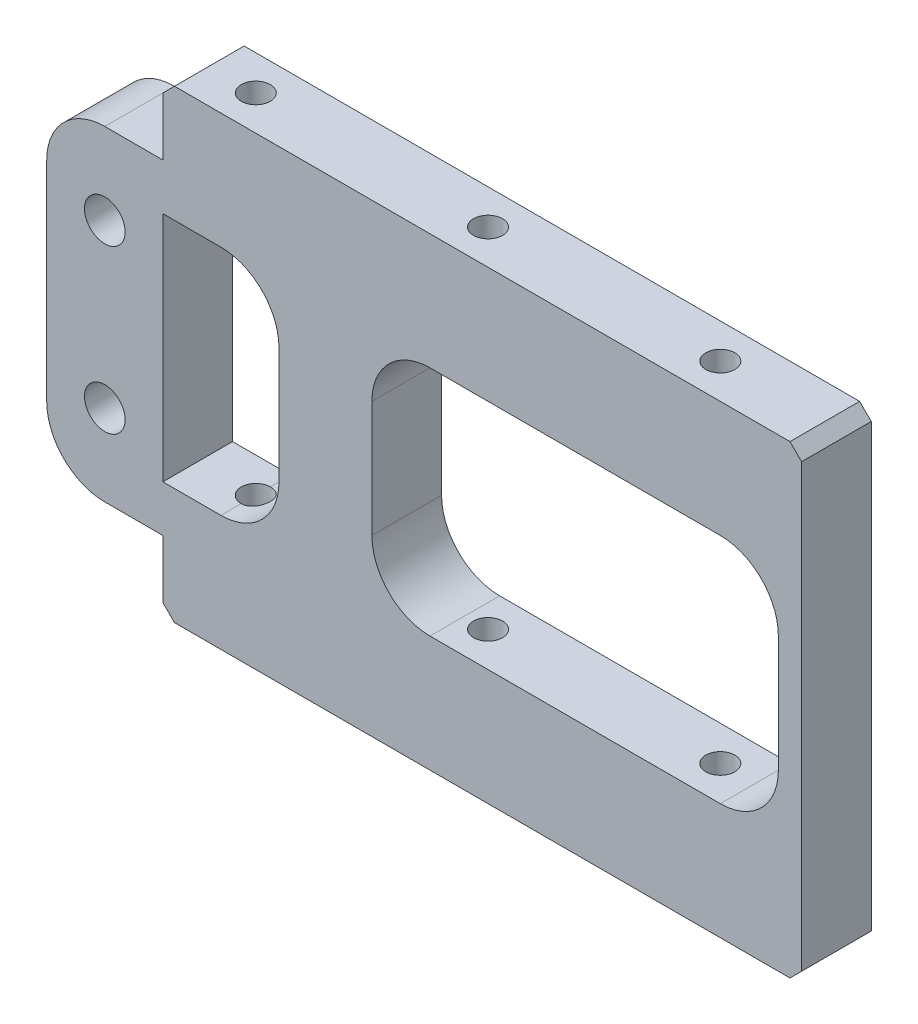
SolidWorks part; units mm, degrees
ref_plane "Front Plane" through (0, 0, 0) normal (0, 0, 1) x (1, 0, 0)
ref_plane "Top Plane" through (0, 0, 0) normal (0, 1, 0) x (1, 0, 0)
ref_plane "Right Plane" through (0, 0, 0) normal (1, 0, 0) x (0, 0, -1)
sketch "Sketch1" plane through (0, 0, 0) normal (0, 1, 0) x (1, 0, 0)
  line L1 (-27.5, 3) -> (27.5, 3)
  line L2 (-27.5, 3) -> (-27.5, -3)
  line L3 (-27.5, -3) -> (27.5, -3)
  line L4 (27.5, 3) -> (27.5, -3)
  line L5 (-27.5, 3) -> (27.5, -3) construction
  line L6 (-27.5, -3) -> (27.5, 3) construction
  point P0 (0, 0)
  dimension "D1" = 6
  dimension "D2" = 55
extrude "Boss-Extrude1" add sketch "Sketch1" along normal blind 40
sketch "Sketch2" plane through (0, 40, 0) normal (0, 1, 0) x (1, 0, 0)
  line L0 (-27.5, 3) -> (-27.5, -3) construction
  line L1 (-55, 0) -> (55, 0) construction
  point P0 (-22.5, 0)
  point P1 (-2.5, 0)
  point P2 (17.5, 0)
  dimension "D1" = 5
  dimension "D2" = 20
  dimension "D3" = 20
hole_wizard "M3 Tapped Hole1" positions "3DSketch4" profile "Sketch6" tap size "M3" standard "ISO" end condition through all
sketch3d "3DSketch4"
  point P0 (-22.5, 40, 0)
  point P3 (-2.5, 40, 0)
  point P6 (17.5, 40, 0)
sketch "Sketch6" plane through (-22.5, 40, 0) normal (1, 0, 0) x (0, 0, 1)
  line L0 (0, 0) -> (0, 40)
  line L1 (0, 40) -> (1.25, 40)
  line L2 (1.25, 40) -> (1.25, 0)
  line L5 (1.25, 0) -> (0, 0)
  line L11 (0, -6.35) -> (0, 107.95) construction
  dimension "Thru Tap Drill Dia." = 2.5
  dimension "Thru Tap Drill Depth" = 40
cosmetic thread "Hole Thread1"
cosmetic thread "Hole Thread2"
cosmetic thread "Hole Thread3"
sketch "Sketch7" plane through (0, 0, -3) normal (0, 0, -1) x (-1, 0, 0)
  line L5 (27.5, 40) -> (27.5, 0) construction
  line L6 (27.5, 30) -> (22.5, 30)
  line L7 (27.5, 30) -> (27.5, 10)
  line L8 (27.5, 10) -> (22.5, 10)
  line L9 (17.5, 25) -> (17.5, 15)
  line L11 (4.5, 30) -> (-20.5, 30)
  line L12 (9.5, 25) -> (9.5, 15)
  line L13 (4.5, 10) -> (-20.5, 10)
  line L14 (-25.5, 25) -> (-25.5, 15)
  line L15 (55, 0) -> (-55, 0) construction
  line L16 (27.5, 40) -> (-27.5, 40) construction
  arc A0 (-20.5, 30) -> (-25.5, 25) centre (-20.5, 25) ccw
  arc A1 (-20.5, 10) -> (-25.5, 15) centre (-20.5, 15) cw
  arc A2 (9.5, 15) -> (4.5, 10) centre (4.5, 15) cw
  arc A3 (4.5, 30) -> (9.5, 25) centre (4.5, 25) cw
  arc A4 (22.5, 10) -> (17.5, 15) centre (22.5, 15) cw
  arc A5 (22.5, 30) -> (17.5, 25) centre (22.5, 25) ccw
  point P18 (-25.5, 10)
  point P21 (9.5, 10)
  point P28 (17.5, 30)
  dimension "D6" = 5
  dimension "D7" = 5
  dimension "D1" = 10
  dimension "D2" = 10
  dimension "D3" = 10
  dimension "D4" = 8
  dimension "D5" = 35
  dimension "D8" = 20
extrude "Cut-Extrude1" cut sketch "Sketch7" against normal blind 40
chamfer "Chamfer1" distance 1 angle 45 4 edges at (27.5, 0, 0) (27.5, 40, 0) (-27.5, 0, 0) (-27.5, 40, 0)
sketch "Sketch9" plane through (0, 0, -3) normal (0, 0, -1) x (-1, 0, 0)
  line L0 (27.5, 39) -> (27.5, 30) construction
  line L1 (27.5, 34) -> (32.5, 34)
  line L2 (27.5, 34) -> (27.5, 6)
  line L3 (27.5, 6) -> (32.5, 6)
  line L4 (37.5, 29) -> (37.5, 11)
  line L5 (-26.5, 40) -> (26.5, 40) construction
  line L6 (55, 0) -> (-55, 0) construction
  arc A0 (32.5, 6) -> (37.5, 11) centre (32.5, 11) ccw
  arc A1 (32.5, 34) -> (37.5, 29) centre (32.5, 29) cw
  circle A2 centre (32.5, 27) radius 1.75
  circle A3 centre (32.5, 13) radius 1.75
  point P14 (37.5, 34)
  point P19 (27.5, 20)
  dimension "D4" = 5
  dimension "D5" = 3.5
  dimension "D1" = 6
  dimension "D2" = 6
  dimension "D3" = 10
  dimension "D6" = 7
  dimension "D7" = 14
  dimension "D8" = 5
extrude "Boss-Extrude4" add sketch "Sketch9" against normal blind 6
